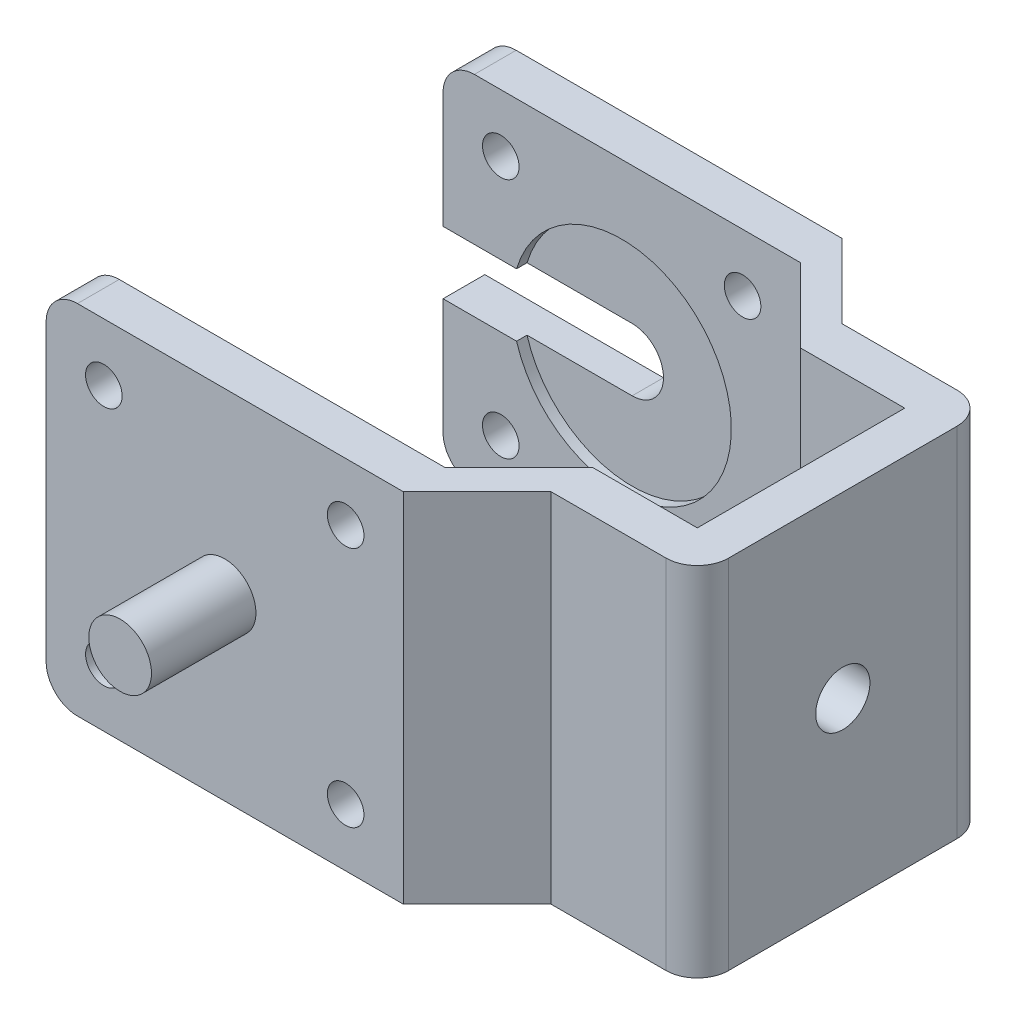
SolidWorks part; units mm, degrees
ref_plane "Front Plane" through (0, 0, 0) normal (0, 0, 1) x (1, 0, 0)
ref_plane "Top Plane" through (0, 0, 0) normal (0, 1, 0) x (1, 0, 0)
ref_plane "Right Plane" through (0, 0, 0) normal (1, 0, 0) x (0, 0, -1)
sketch "Sketch1" plane through (0, 0, 0) normal (0, 1, 0) x (1, 0, 0)
  line L0 (0, 0) -> (34.2, 0)
  line L1 (34.2, 0) -> (41.2711, -7.0711)
  line L2 (41.2711, -7.0711) -> (51.2711, -7.0711)
  line L3 (0, -34) -> (34.2, -34)
  line L4 (34.2, -34) -> (41.2711, -26.9289)
  line L5 (41.2711, -26.9289) -> (51.2711, -26.9289)
  line L6 (51.2711, -7.0711) -> (51.2711, -26.9289)
  line L7 (0, 0) -> (0, 4)
  line L8 (0, 4) -> (34.2, 4)
  line L10 (51.2711, -3.0711) -> (41.2711, -3.0711)
  line L11 (41.2711, -3.0711) -> (34.2, 4)
  line L12 (51.2711, -3.0711) -> (55.2711, -3.0711)
  line L13 (55.2711, -3.0711) -> (55.2711, -26.9289)
  line L14 (55.2711, -26.9289) -> (55.2711, -30.9289)
  line L15 (55.2711, -30.9289) -> (41.2711, -30.9289)
  line L16 (0, -34) -> (0, -38)
  line L17 (0, -38) -> (34.2, -38)
  line L18 (34.2, -38) -> (41.2711, -30.9289)
  dimension "D7" = 34
  dimension "D1" = 34.2
  dimension "D2" = 10
  dimension "D3" = 10
  dimension "D4" = 34.2
  dimension "D5" = 10
  dimension "D6" = 10
  dimension "D8" = 135
  dimension "D9" = 135
  dimension "D10" = 4
  dimension "D11" = 34.2
  dimension "D12" = 4
  dimension "D13" = 10
  dimension "D14" = 4
  dimension "D15" = 4
  dimension "D16" = 14
  dimension "D17" = 4
  dimension "D18" = 34.2
extrude "Boss-Extrude1" add sketch "Sketch1" along normal blind 34.2
sketch "Sketch2" plane through (0, 0, -4) normal (0, 0, -1) x (-1, 0, 0)
  line L0 (-17.1, 34.2) -> (-17.1, 0)
  line L1 (-34.2, 34.2) -> (0, 34.2) construction
  line L2 (-34.2, 0) -> (0, 0) construction
  line L3 (-34.2, 17.1) -> (0, 17.1)
  line L4 (-34.2, 34.2) -> (-34.2, 0) construction
  line L5 (0, 34.2) -> (0, 0) construction
  line L7 (-28.675, 28.675) -> (-5.525, 28.675)
  line L8 (-28.675, 28.675) -> (-28.675, 5.525)
  line L9 (-28.675, 5.525) -> (-5.525, 5.525)
  line L10 (-5.525, 28.675) -> (-5.525, 5.525)
  line L11 (-28.675, 28.675) -> (-5.525, 5.525) construction
  line L12 (-28.675, 5.525) -> (-5.525, 28.675) construction
  circle A0 centre (-28.675, 28.675) radius 1.75
  circle A1 centre (-5.525, 28.675) radius 1.75
  circle A2 centre (-5.525, 5.525) radius 1.75
  circle A3 centre (-28.675, 5.525) radius 1.75
  circle A4 centre (-17.1, 17.1) radius 3
  point P12 (-17.1, 17.1)
  dimension "D2" = 3.5
  dimension "D3" = 3.5
  dimension "D4" = 3.5
  dimension "D5" = 3.5
  dimension "D6" = 6
  dimension "D1" = 23.15
sketch "Sketch3" plane through (0, 0, 0) normal (0, 0, 1) x (1, 0, 0)
  circle A0 centre (17.1, 17.1) radius 10.5
  dimension "D1" = 21
extrude "Cut-Extrude2" cut sketch "Sketch2" against normal up to surface (4 mm away) contours A2 | A3 | A4 | A1 | A0 up to face at (17.1, 17.1, 0)
extrude "Cut-Extrude3" cut sketch "Sketch3" against normal blind 1 contours A0
sketch "Sketch4" plane through (0, 0, 38) normal (0, 0, 1) x (1, 0, 0)
  line L0 (17.1, 34.2) -> (17.1, 0)
  line L1 (0, 34.2) -> (34.2, 34.2) construction
  line L2 (0, 0) -> (34.2, 0) construction
  line L3 (0, 17.1) -> (34.2, 17.1)
  line L4 (0, 34.2) -> (0, 0) construction
  line L5 (34.2, 34.2) -> (34.2, 0) construction
sketch "Sketch5" plane through (0, 0, 38) normal (0, 0, 1) x (1, 0, 0)
  line L0 (17.1, 34.2) -> (17.1, 0) construction
  line L1 (5.525, 28.675) -> (28.675, 28.675)
  line L2 (5.525, 28.675) -> (5.525, 5.525)
  line L3 (5.525, 5.525) -> (28.675, 5.525)
  line L4 (28.675, 28.675) -> (28.675, 5.525)
  line L5 (5.525, 28.675) -> (28.675, 5.525) construction
  line L6 (5.525, 5.525) -> (28.675, 28.675) construction
  circle A0 centre (28.675, 28.675) radius 1.75
  circle A1 centre (5.525, 28.675) radius 1.75
  circle A2 centre (5.525, 5.525) radius 1.75
  circle A3 centre (28.675, 5.525) radius 1.75
  point P0 (17.1, 17.1)
  dimension "D2" = 3.5
  dimension "D3" = 3.5
  dimension "D4" = 1.75
  dimension "D5" = 1.75
  dimension "D1" = 23.15
extrude "Cut-Extrude7" cut sketch "Sketch5" against normal up to surface (4 mm away) contours A3 | A2 | A1 | A0 up to face at (17.1, 17.1, 34)
fillet "Fillet2" radius 3 4 edges at (0, 0, -2) (0, 0, 36) (0, 34.2, 36) (0, 34.2, -2)
fillet "Fillet3" radius 3 2 edges at (55.2711, 17.1, 3.0711) (55.2711, 17.1, 30.9289)
sketch "Sketch12" plane through (55.2711, 0, 0) normal (1, 0, 0) x (0, 0, -1)
  line L0 (-17, 34.2) -> (-17, 0)
  line L1 (-27.9289, 34.2) -> (-6.0711, 34.2) construction
  line L2 (-27.9289, 0) -> (-6.0711, 0) construction
  circle A0 centre (-17, 17.1) radius 2.595
  dimension "D1" = 5.19
extrude "Cut-Extrude8" cut sketch "Sketch12" against normal up to surface (4 mm away) contours A0 up to face at (51.2711, 17.1, 17)
sketch "Sketch14" plane through (0, 0, -4) normal (0, 0, -1) x (-1, 0, 0)
  line L0 (-17.1, 20.1) -> (0, 20.1)
  line L1 (0, 31.2) -> (0, 3) construction
  line L2 (-17.1, 14.1) -> (0, 14.1)
  line L3 (0, 14.1) -> (0, 20.1)
  line L4 (-17.1, 20.1) -> (-17.1, 14.1)
  circle A0 centre (-17.1, 17.1) radius 3 construction
extrude "Cut-Extrude9" cut sketch "Sketch14" against normal up to surface (4 mm away) up to face at (27.6, 17.1, 0)
sketch "Sketch15" plane through (0, 0, 38) normal (0, 0, 1) x (1, 0, 0)
  circle A0 centre (17.0865, 17.0847) radius 3
  dimension "D1" = 6
extrude "Boss-Extrude2" add sketch "Sketch15" along normal blind 10
